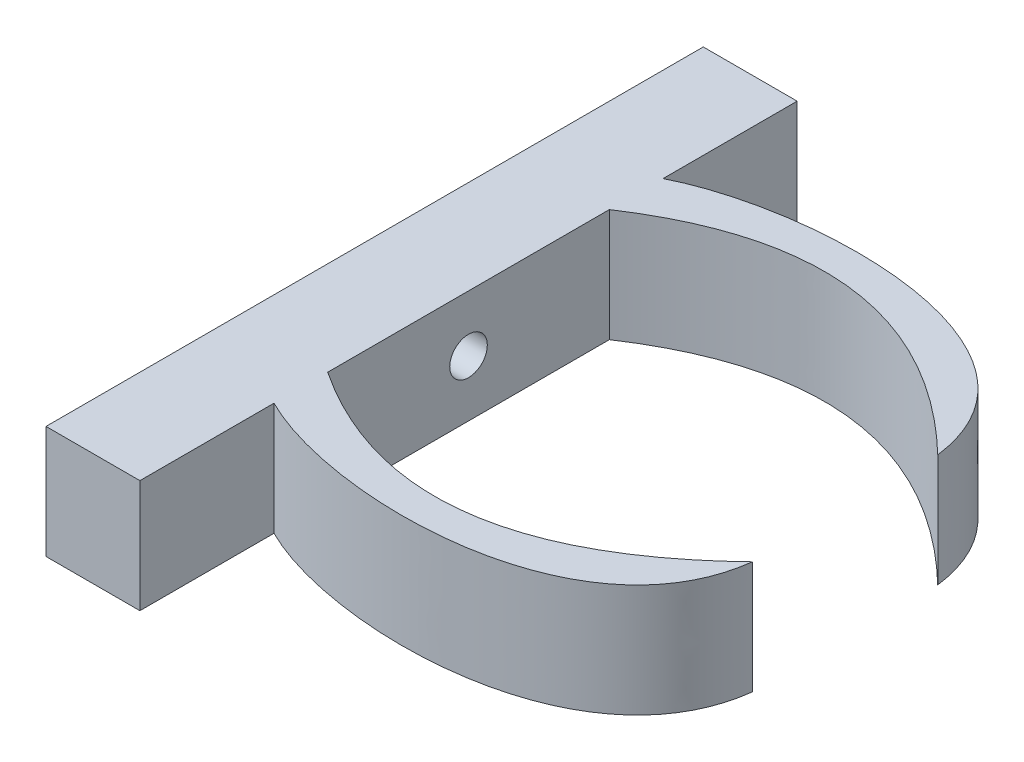
SolidWorks part; units mm, degrees
ref_plane "Front Plane" through (0, 0, 0) normal (0, 0, 1) x (1, 0, 0)
ref_plane "Top Plane" through (0, 0, 0) normal (0, 1, 0) x (1, 0, 0)
ref_plane "Right Plane" through (0, 0, 0) normal (1, 0, 0) x (0, 0, -1)
sketch "Sketch1" plane through (0, 0, 0) normal (1, 0, 0) x (0, 0, -1)
  line L1 (-35, 6) -> (35, 6)
  line L2 (-35, 6) -> (-35, -6)
  line L3 (-35, -6) -> (35, -6)
  line L4 (35, 6) -> (35, -6)
  line L5 (-35, 6) -> (35, -6) construction
  line L6 (-35, -6) -> (35, 6) construction
  point P0 (0, 0)
  dimension "D1" = 70
  dimension "D2" = 12
extrude "Boss-Extrude1" add sketch "Sketch1" along normal blind 10
sketch "Sketch2" plane through (0, 6, 0) normal (0, 1, 0) x (1, 0, 0)
  line L0 (10, 0) -> (41.6373, 0)
  line L1 (10, 35) -> (10, -35) construction
  line L2 (10, 15) -> (10, 0)
  line L3 (10, -20.7176) -> (10, -15)
  line L4 (10, 15) -> (10, 20.7176)
  spline S0 degree 2 poles (10, 15) (30.648, 28.6689) (50.1057, 9.8683) knots 0 0 0 1 1 1
  spline S1 degree 3 poles (10, 20.7176) (21.3603, 26.4517) (47.9847, 26.7993) (50.1057, 9.8683) knots 0 0 0 0 1 1 1 1
  spline S2 degree 3 poles (10, -20.7176) (21.3603, -26.4517) (47.9847, -26.7993) (50.1057, -9.8683) knots 0 0 0 0 1 1 1 1
  spline S3 degree 2 poles (10, -15) (30.648, -28.6689) (50.1057, -9.8683) knots 0 0 0 1 1 1
  line M8 (10, -35) -> (10, 35)
  dimension "D1" = 15
extrude "Boss-Extrude2" add sketch "Sketch2" against normal blind 12 contours S3 S2 M8 | S1 S0 M8
sketch "Sketch3" plane through (0, 0, 0) normal (-1, 0, 0) x (0, 0, 1)
  circle A0 centre (0, 0) radius 2
  dimension "D1" = 4
extrude "Cut-Extrude1" cut sketch "Sketch3" against normal blind 12
